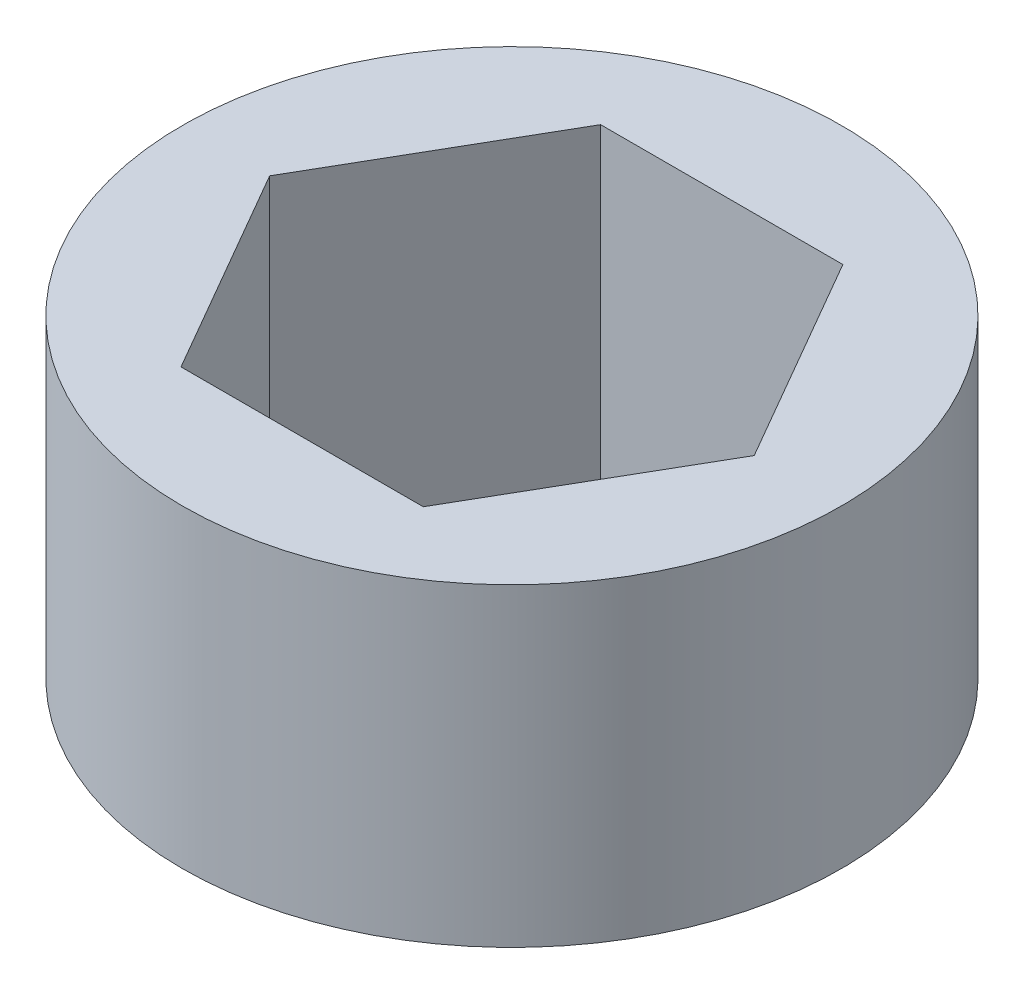
SolidWorks part; units mm, degrees
ref_plane "Front Plane" through (0, 0, 0) normal (0, 0, 1) x (1, 0, 0)
ref_plane "Top Plane" through (0, 0, 0) normal (0, 1, 0) x (1, 0, 0)
ref_plane "Right Plane" through (0, 0, 0) normal (1, 0, 0) x (0, 0, -1)
sketch "Sketch1" plane through (0, 0, 0) normal (0, 1, 0) x (1, 0, 0)
  line L1 (7.347, 0) -> (3.6735, 6.3627)
  line L2 (3.6735, 6.3627) -> (-3.6735, 6.3627)
  line L3 (-3.6735, 6.3627) -> (-7.347, 0)
  line L4 (-7.347, 0) -> (-3.6735, -6.3627)
  line L5 (-3.6735, -6.3627) -> (3.6735, -6.3627)
  line L6 (3.6735, -6.3627) -> (7.347, 0)
  circle A0 centre (0, 0) radius 9.9949
  circle A1 centre (0, 0) radius 6.3627 construction
  dimension "D1" = 19.9898
  dimension "D2" = 12.7254
extrude "Boss-Extrude1" add sketch "Sketch1" along normal blind 9.525
